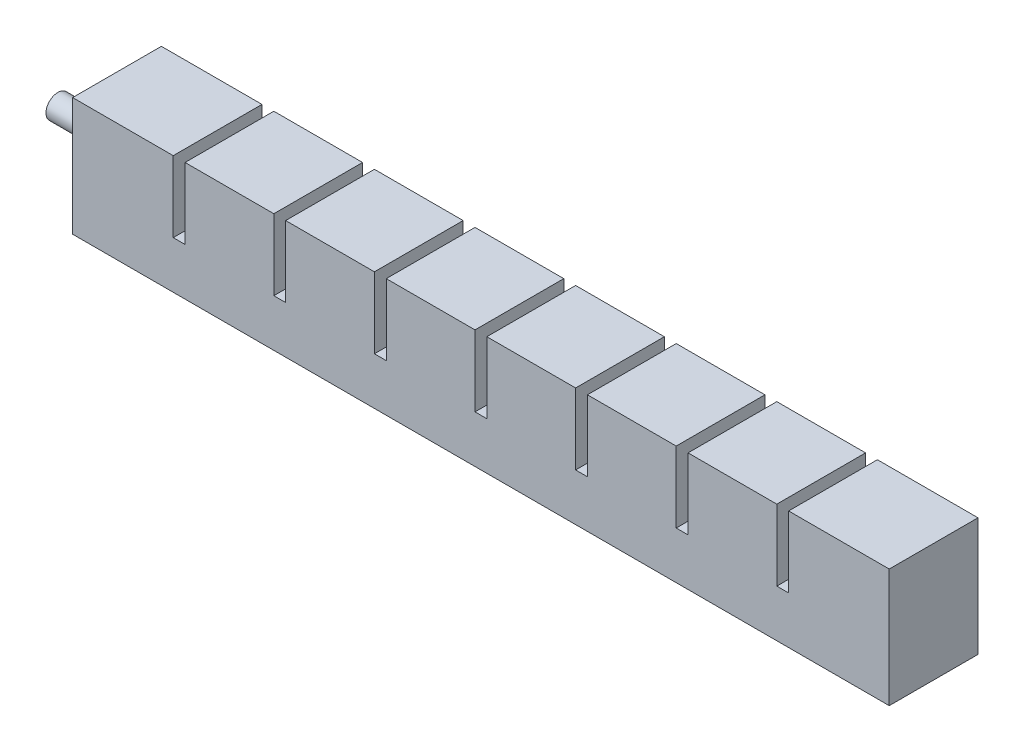
SolidWorks part; units mm, degrees
ref_plane "Front Plane" through (0, 0, 0) normal (0, 0, 1) x (1, 0, 0)
ref_plane "Top Plane" through (0, 0, 0) normal (0, 1, 0) x (1, 0, 0)
ref_plane "Right Plane" through (0, 0, 0) normal (1, 0, 0) x (0, 0, -1)
sketch "Sketch1" plane through (0, 0, 0) normal (0, 0, 1) x (1, 0, 0)
  line L1 (0, 0) -> (15, 0)
  line L2 (0, 0) -> (0, 15)
  line L3 (0, 15) -> (15, 15)
  line L4 (15, 0) -> (15, 15)
  dimension "D1" = 15
  dimension "D2" = 15
extrude "Boss-Extrude1" add sketch "Sketch1" along normal blind 15
sketch "Sketch2" plane through (0, 0, 0) normal (0, -1, 0) x (1, 0, 0)
  line L0 (0, 15) -> (15, 15) construction
  line L1 (4, 11) -> (11, 11)
  line L2 (4, 11) -> (4, 4)
  line L3 (4, 4) -> (11, 4)
  line L4 (11, 11) -> (11, 4)
  line L5 (15, 15) -> (15, 0) construction
  line L6 (0, 0) -> (15, 0) construction
  line L7 (0, 15) -> (0, 0) construction
  dimension "D1" = 4
  dimension "D2" = 4
  dimension "D3" = 4
  dimension "D4" = 4
extrude "Cut-Extrude1" cut sketch "Sketch2" against normal blind 11
sketch "Sketch3" plane through (15, 0, 0) normal (1, 0, 0) x (0, 0, -1)
  line L0 (0, 0) -> (0, 15) construction
  line L1 (-15, 0) -> (0, 0)
  line L2 (-15, 0) -> (-15, 3)
  line L3 (-15, 3) -> (0, 3)
  line L4 (0, 0) -> (0, 3)
  dimension "D1" = 3
extrude "Boss-Extrude2" add sketch "Sketch3" along normal blind 2
pattern_linear "LPattern1" count 8 spacing 17 along (1, 0, 0) of bodies 103
combine bodies "Combine1" operation type add bodies to combine 109 110 104 105 106 107 103 108
sketch "Sketch9" plane through (134, 0, 0) normal (1, 0, 0) x (0, 0, -1)
  line L1 (-15, 15) -> (0, 15)
  line L2 (-15, 15) -> (-15, 3)
  line L3 (-15, 3) -> (0, 3)
  line L4 (0, 15) -> (0, 3)
extrude "Boss-Extrude3" add sketch "Sketch9" along normal up to surface (2 mm away) up to face at (136, 1.5, 7.5)
sketch "Sketch10" plane through (0, 0, 0) normal (-1, 0, 0) x (0, 0, 1)
  line L1 (0, 15) -> (15, 15)
  line L2 (0, 15) -> (0, 0)
  line L3 (0, 0) -> (15, 0)
  line L4 (15, 15) -> (15, 0)
extrude "Boss-Extrude4" add sketch "Sketch10" along normal blind 2
ref_point "Point3"
sketch "Sketch11" plane through (0, 0, 0) normal (0, -1, 0) x (1, 0, 0)
  line L0 (11, 4) -> (11, 11) construction
  line L1 (123, 8.75) -> (11, 8.75)
  line L2 (123, 8.75) -> (123, 6.25)
  line L3 (123, 6.25) -> (11, 6.25)
  line L4 (11, 8.75) -> (11, 6.25)
  line L5 (123, 8.75) -> (11, 6.25) construction
  line L6 (123, 6.25) -> (11, 8.75) construction
  point P0 (67, 7.5)
  dimension "D1" = 2.5
extrude "Cut-Extrude2" cut sketch "Sketch11" against normal blind 2
sketch "Sketch12" plane through (0, 0, 0) normal (0, -1, 0) x (1, 0, 0)
  line L1 (-2, 15) -> (136, 15)
  line L2 (-2, 15) -> (-2, 0)
  line L3 (-2, 0) -> (136, 0)
  line L4 (136, 15) -> (136, 0)
extrude "Boss-Extrude5" add sketch "Sketch12" along normal blind 3
sketch "Sketch13" plane through (0, -3, 0) normal (0, -1, 0) x (1, 0, 0)
  line L1 (-2, 15) -> (136, 15)
  line L2 (-2, 15) -> (-2, 0)
  line L3 (-2, 0) -> (136, 0)
  line L4 (136, 15) -> (136, 0)
extrude "Boss-Extrude6" add sketch "Sketch13" along normal blind 2
ref_point "Point4"
sketch "Sketch14" plane through (-2, 0, 0) normal (-1, 0, 0) x (0, 0, 1)
  circle A0 centre (7.5, 5) radius 2
  dimension "D1" = 4
extrude "Boss-Extrude7" add sketch "Sketch14" along normal blind 10
sketch "Sketch15" plane through (-12, 0, 0) normal (-1, 0, 0) x (0, 0, 1)
  circle A0 centre (7.5, 5) radius 1
  dimension "D1" = 2
extrude "Cut-Extrude3" cut sketch "Sketch15" against normal blind 18
